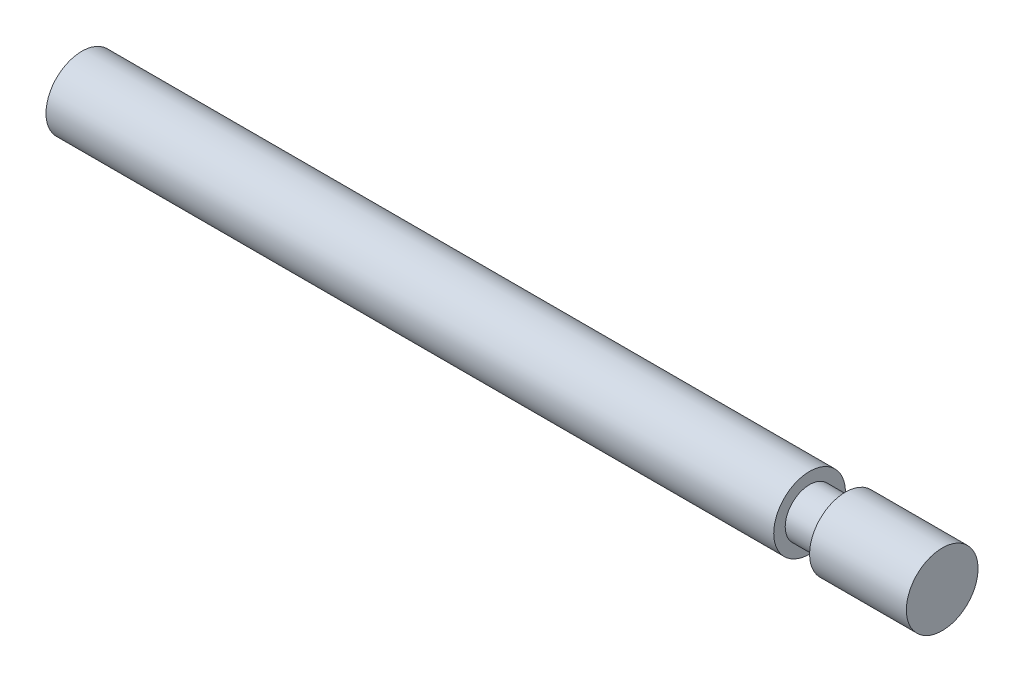
SolidWorks part; units mm, degrees
ref_plane "Plano frontal" through (0, 0, 0) normal (0, 0, 1) x (1, 0, 0)
ref_plane "Plano superior" through (0, 0, 0) normal (0, 1, 0) x (1, 0, 0)
ref_plane "Plano direito" through (0, 0, 0) normal (1, 0, 0) x (0, 0, -1)
sketch "Esboço1" plane through (0, 0, 0) normal (0, 1, 0) x (1, 0, 0)
  line L0 (-67.0337, 0) -> (61.8316, 0) construction
  line L1 (-60, 0) -> (-60, -2.5)
  line L2 (-60, -2.5) -> (-9.25, -2.5)
  line L3 (-9.25, -2.5) -> (-9.25, -1.7)
  line L4 (-9.25, -1.7) -> (-6.75, -1.7)
  line L5 (-6.75, -1.7) -> (-6.75, -2.5)
  line L6 (-6.75, -2.5) -> (0, -2.5)
  line L7 (0, -2.5) -> (0, 0)
  line L8 (-60, 0) -> (0, 0)
  dimension "D1" = 60
  dimension "D2" = 5
  dimension "D3" = 3.4
  dimension "D4" = 5
  dimension "D5" = 6.75
  dimension "D6" = 9.25
revolve "Revolução1" add sketch "Esboço1" angle 360 about L0
